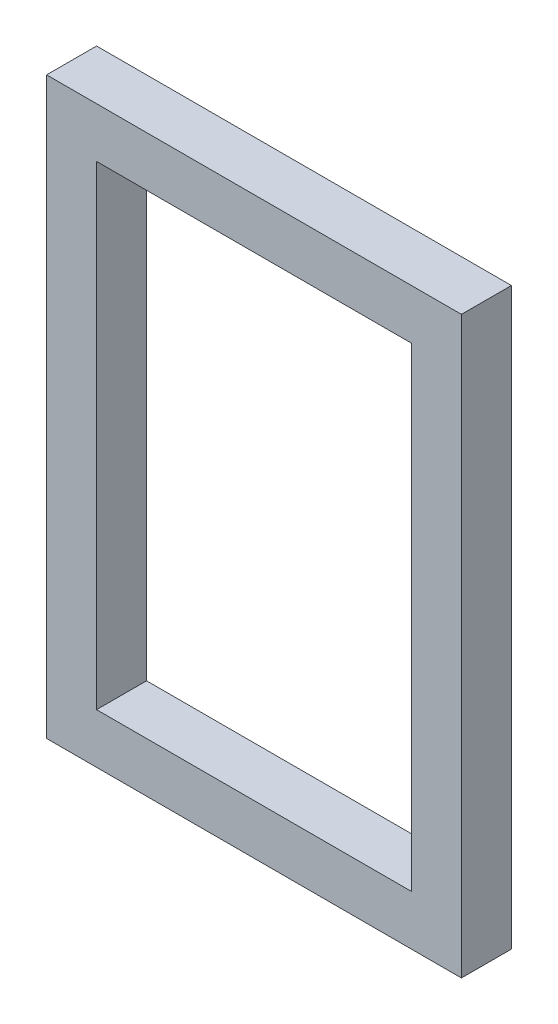
SolidWorks part; units mm, degrees
material "Nickel"
ref_plane "Front Plane" through (0, 0, 0) normal (0, 0, 1) x (1, 0, 0)
ref_plane "Top Plane" through (0, 0, 0) normal (0, 1, 0) x (1, 0, 0)
ref_plane "Right Plane" through (0, 0, 0) normal (1, 0, 0) x (0, 0, -1)
sketch "Sketch1" plane through (0, 0, 0) normal (0, 0, 1) x (1, 0, 0)
  line L1 (-10.541, -14.605) -> (10.541, -14.605)
  line L2 (-10.541, -14.605) -> (-10.541, 14.605)
  line L3 (-10.541, 14.605) -> (10.541, 14.605)
  line L4 (10.541, -14.605) -> (10.541, 14.605)
  line L5 (-10.541, -14.605) -> (10.541, 14.605) construction
  line L6 (-10.541, 14.605) -> (10.541, -14.605) construction
  point P0 (0, 0)
  dimension "D1" = 29.21
  dimension "D2" = 21.082
extrude "Boss-Extrude1" add sketch "Sketch1" along normal blind 2.54
sketch "Sketch2" plane through (0, 0, 2.54) normal (0, 0, 1) x (1, 0, 0)
  line L0 (-10.541, 14.605) -> (-10.541, -14.605) construction
  line L1 (-8.001, -12.065) -> (8.001, -12.065)
  line L2 (-8.001, -12.065) -> (-8.001, 12.065)
  line L3 (-8.001, 12.065) -> (8.001, 12.065)
  line L4 (8.001, -12.065) -> (8.001, 12.065)
  line L5 (-8.001, -12.065) -> (8.001, 12.065) construction
  line L6 (-8.001, 12.065) -> (8.001, -12.065) construction
  line L7 (10.541, -14.605) -> (10.541, 14.605) construction
  line L8 (10.541, 14.605) -> (-10.541, 14.605) construction
  point P0 (0, 0)
  dimension "D1" = 2.54
  dimension "D2" = 2.54
  dimension "D3" = 2.54
extrude "Cut-Extrude1" cut sketch "Sketch2" against normal through all
